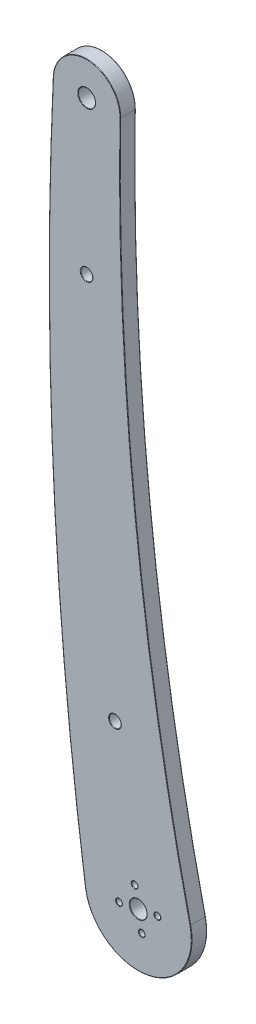
SolidWorks part; units mm, degrees
ref_plane "Front Plane" through (0, 0, 0) normal (0, 0, 1) x (1, 0, 0)
ref_plane "Top Plane" through (0, 0, 0) normal (0, 1, 0) x (1, 0, 0)
ref_plane "Right Plane" through (0, 0, 0) normal (1, 0, 0) x (0, 0, -1)
sketch "Sketch1" plane through (0, 0, 0) normal (0, 0, 1) x (1, 0, 0)
  line L0 (-20.22, 57.58) -> (-37.0777, 278.939) construction
  line L1 (-20.22, 57.58) -> (-37.0777, 278.939) construction
  line L2 (-20.22, 57.58) -> (-17.0242, 40.3743) construction
  line L3 (-20.22, 57.58) -> (-3.0143, 60.7758) construction
  line L4 (-20.22, 57.58) -> (-23.4158, 74.7857) construction
  line L5 (-20.22, 57.58) -> (-37.4257, 54.3842) construction
  circle A0 centre (-37.0777, 278.939) radius 11 construction
  circle A1 centre (-37.0777, 278.939) radius 11 construction
  circle A2 centre (-20.22, 57.58) radius 17.5 construction
  circle A3 centre (-20.22, 57.58) radius 17.5 construction
  circle A4 centre (-20.22, 57.58) radius 2.8
  circle A5 centre (-37.0777, 278.939) radius 2.8
  arc A8 (-26.0792, 278.7566) -> (-3.1679, 61.514) centre (873.7971, 263.8316) ccw
  arc A9 (-48.0656, 279.4542) -> (-37.5474, 55.1282) centre (1150.6174, 223.2484) ccw
  arc A10 (-37.0777, 278.939) -> (-20.22, 57.58) centre (1087.6295, 253.27) ccw construction
  arc A11 (-48.0656, 279.4542) -> (-26.0792, 278.7566) centre (-37.0777, 278.939) cw
  arc A12 (-37.5474, 55.1282) -> (-3.1679, 61.514) centre (-20.22, 57.58) ccw
  circle A13 centre (-37.1074, 228.939) radius 1.95
  circle A15 centre (-27.821, 106.9989) radius 1.95
  circle A17 centre (-19.0531, 51.2975) radius 1
  circle A18 centre (-26.5025, 56.4131) radius 1
  circle A19 centre (-21.3869, 63.8625) radius 1
  circle A20 centre (-13.9375, 58.7469) radius 1
  point P19 (-37.1074, 228.939)
  point P20 (-27.821, 106.9989)
  dimension "D1" = 5.6
  dimension "D2" = 5.6
  dimension "D3" = 1200
  dimension "D4" = 1125
  dimension "D5" = 900
  dimension "D8" = 3.9
  dimension "D9" = 2
  dimension "D6" = 50
  dimension "D7" = 50
  dimension "D10" = 6.39
  dimension "D11" = 6.39
extrude "Boss-Extrude1" add sketch "Sketch1" against normal blind 5
fillet "Fillet1" radius 0.15 24 edges at (-48.0657, 167.0447, -5) (-17.0242, 40.3743, -5) (-21.2391, 169.4376, -5) (-36.7288, 289.9335, -5) (-17.42, 57.58, -5) (-34.2777, 278.939, -5) (-25.871, 106.9989, -5) (-35.1574, 228.939, -5) (-21.2391, 169.4376, 0) (-17.0242, 40.3743, 0) (-48.0657, 167.0447, 0) (-36.7288, 289.9335, 0) (-17.42, 57.58, 0) (-34.2777, 278.939, 0) (-25.871, 106.9989, 0) (-35.1574, 228.939, 0) (-18.0531, 51.2975, -5) (-18.0531, 51.2975, 0) (-25.5025, 56.4131, -5) (-25.5025, 56.4131, 0) (-22.3869, 63.8625, -5) (-14.9375, 58.7469, -5) (-22.3869, 63.8625, 0) (-14.9375, 58.7469, 0)
